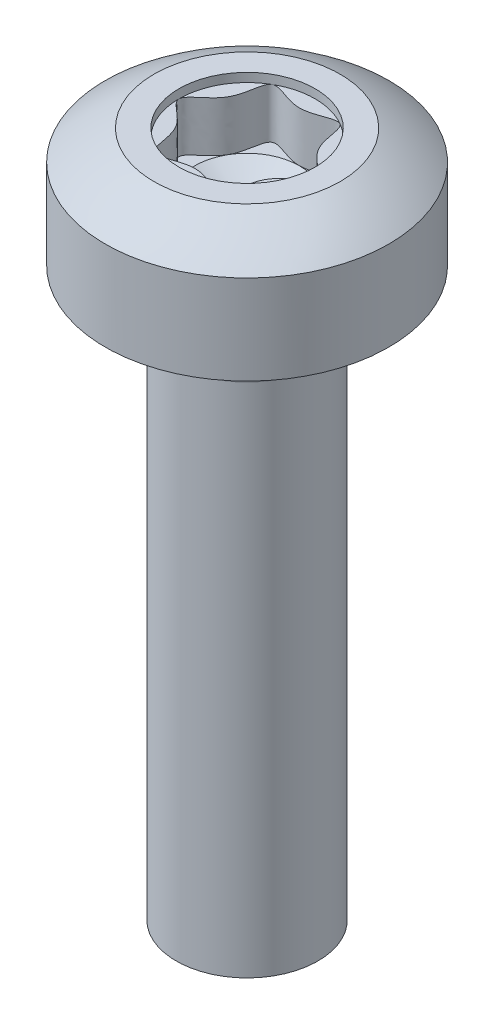
SolidWorks part; units mm, degrees
material "AISI 316L Acero inoxidable"
ref_plane "Front" through (0, 0, 0) normal (0, 0, 1) x (1, 0, 0)
ref_plane "Top" through (0, 0, 0) normal (0, 1, 0) x (1, 0, 0)
ref_plane "Right" through (0, 0, 0) normal (1, 0, 0) x (0, 0, -1)
sketch "Sketch1" plane through (0, 0, 0) normal (0, 0, 1) x (1, 0, 0)
  line L0 (0, 0) -> (0, 34.6184) construction
  line L1 (0, 0) -> (1.25, 0)
  line L2 (1.25, 0) -> (1.25, 10)
  line L3 (1.25, 10) -> (2.5, 10)
  line L4 (2.5, 10) -> (2.5, 12.1)
  line L5 (2.5, 12.1) -> (0, 12.1)
  line L6 (0, 12.1) -> (0, 0)
  line L7 (2.5, 10) -> (2.95, 10) construction
  line L8 (2.95, 10) -> (2.95, 0.9) construction
  dimension "HEAD_DIA" = 5
  dimension "HEAD_HT" = 2.1
  dimension "LENGTH" = 10
  dimension "DIA" = 2.5
  dimension "pitch" = 0.45
  dimension "thread_length" = 9.1
revolve "BODY" add sketch "Sketch1" angle 360 about L0
cosmetic thread "ThreadCosmetic" [suppressed] parameters "D1"=9.1, "D2"=2.0129
sketch "Sketch2" plane through (0, 0, 0) normal (0, 0, 1) x (1, 0, 0)
  line L0 (2.5, 11.575) -> (0, 8.4525) construction
  line L3 (2.5, 10) -> (2.5, 12.1) construction
  line L4 (0, 0) -> (0, 34.6184) construction
  line L5 (0, 12.4525) -> (0, 12.9347)
  line L6 (4, 8.4525) -> (4, 12.9347)
  line L7 (4, 12.9347) -> (0, 12.9347)
  line L8 (0, 12.9347) -> (4, 12.9347)
  arc A0 (4, 8.4525) -> (0, 12.4525) centre (0, 8.4525) ccw
  dimension "SPHERE_DIA" = 4
  dimension "D1" = 0.525
  dimension "D2" = 0.4822
revolve "HEAD-CUT" cut sketch "Sketch2" angle 360 about axis through (0, 0, 0) along (0, 1, 0)
sketch "Sketch4" plane through (0, 0, 0) normal (0, 0, 1) x (1, 0, 0)
  line L0 (-1.25, 9.1) -> (-1.1886, 9.9)
  line L1 (-1.25, 10) -> (-1.25, 0) construction
  line L2 (-1.25, 10) -> (-1.25, 9.1)
  arc A0 (-1.1886, 9.9) -> (-1.25, 10) centre (-1.2884, 9.9076) ccw
  dimension "CONER_RAD" = 0.1
  dimension "D1" = 0.1
  dimension "GAP" = 0.9
revolve "GAP" cut sketch "Sketch4" angle 360 about axis through (0, 0, 0) along (0, 1, 0)
sketch "Sketch5" plane through (0, 12.1, 0) normal (0, 1, 0) x (-1, 0, 0)
  line L0 (0, 0.9231) -> (0, 0) construction
  line L1 (0, 0) -> (0.6, 1.0392) construction
  line L2 (0.6, 1.0392) -> (-0.6, 1.0392) construction
  line L3 (-0.6, 1.0392) -> (-1.2, 0) construction
  line L4 (-1.2, 0) -> (-0.6, -1.0392) construction
  line L5 (-0.6, -1.0392) -> (0.6, -1.0392) construction
  line L6 (0.6, -1.0392) -> (1.2, 0) construction
  line L7 (1.2, 0) -> (0.6, 1.0392) construction
  line L8 (0, 0.9231) -> (-0.7994, 0.4615) construction
  line L9 (-0.7994, 0.4615) -> (-0.7994, -0.4615) construction
  line L10 (-0.7994, -0.4615) -> (0, -0.9231) construction
  line L11 (0, -0.9231) -> (0.7994, -0.4615) construction
  line L12 (0.7994, -0.4615) -> (0.7994, 0.4615) construction
  line L13 (0.7994, 0.4615) -> (0, 0.9231) construction
  circle A0 centre (0, 0) radius 0.9231 construction
  circle A1 centre (0, 0) radius 1.2
  spline S0 degree 3 poles (0.7387, 1.2795) (0, 0.7449) (-0.7387, 1.2795) (-0.6451, 0.3724) (-1.4775, 0) (-0.6451, -0.3724) (-0.7387, -1.2795) (0, -0.7449) (0.7387, -1.2795) (0.6451, -0.3724) (1.4775, 0) (0.6451, 0.3724) (0.7387, 1.2795) (0, 0.7449) (-0.7387, 1.2795) knots -0.25 -0.166667 -0.083333 0 0.083333 0.166667 0.25 0.333333 0.416667 0.5 0.583333 0.666667 0.75 0.833333 0.916667 1 1.083333 1.166667 1.25 only from (0, 0.9231) to (0, 0.9231)
  dimension "slot_dia" = 2.4
  dimension "D3" = 1.8462
  dimension "D1" = 30
extrude "Recess-Cut-Extrude1" cut sketch "Sketch5" against normal blind 1.04
sketch "Sketch3" plane through (0, 0, 0) normal (0, 0, 1) x (1, 0, 0)
  line L0 (0, 10.5271) -> (0.9231, 11.06)
  line L1 (0, 0) -> (0, 34.6184) construction
  line L2 (0.9231, 11.06) -> (0, 11.06)
  line L3 (0, 11.06) -> (0, 10.5271)
  dimension "D1" = 60
  dimension "DRILL_RAD" = 0.9231
  dimension "SLOT_DEP" = 1.04
revolve "DRILL-CUT" cut sketch "Sketch3" angle 360 about axis through (0, 0, 0) along (0, 1, 0)
sketch "Sketch6" plane through (0, 0, 0) normal (0, 0, 1) x (1, 0, 0)
  line L0 (1.25, 0) -> (1.0064, 0.1406)
  line L1 (1.0064, 0.1406) -> (1.25, 0.2812)
  line L4 (1.25, 0.2812) -> (1.25, 0)
  line L5 (0, 0) -> (0, 34.6184) construction
  dimension "D1" = 1.0064
revolve "ThreadSchematic" [suppressed] cut sketch "Sketch6" angle 360 about axis through (0, 0, 0) along (0, 1, 0)
pattern_linear "ThdSchPat" [suppressed] count 20 spacing 0.45 along (0, 1, 0)
sketch "Sketch7" plane through (0, 12.1, 0) normal (0, 1, 0) x (-1, 0, 0)
  circle A0 centre (0, 0) radius 1.2
  dimension "D1" = 2.4
extrude "Recess-Cut-Extrude2" cut sketch "Sketch7" against normal blind 0.156
equation "\"D1@Sketch2\" = \"HEAD_HT@Sketch1\" * 0.25"
equation "\"D1@Sketch4\" = \"CONER_RAD@Sketch4\""
equation "\"D1@Recess-Cut-Extrude1\" = \"SLOT_DEP@Sketch3\""
equation "\"D1@Sketch7\" = \"slot_dia@Sketch5\""
equation "\"D1@Recess-Cut-Extrude2\" = \"SLOT_DEP@Sketch3\" * 0.15"
equation "\"D3@Sketch5\" = \"slot_dia@Sketch5\" / 1.3"
equation "\"DRILL_RAD@Sketch3\" = \"D3@Sketch5\" * 0.5"
equation "\"D1@ThreadCosmetic\" = \"thread_length@Sketch1\""
equation "\"D2@ThreadCosmetic\" = \"DIA@Sketch1\" - 1.0825 * \"pitch@Sketch1\""
equation "\"D1@Sketch6\" = \"D2@ThreadCosmetic\" / 2"
equation "\"D3@ThdSchPat\" = \"pitch@Sketch1\""
equation "\"D1@ThdSchPat\" = \"thread_length@Sketch1\" / \"pitch@Sketch1\""
